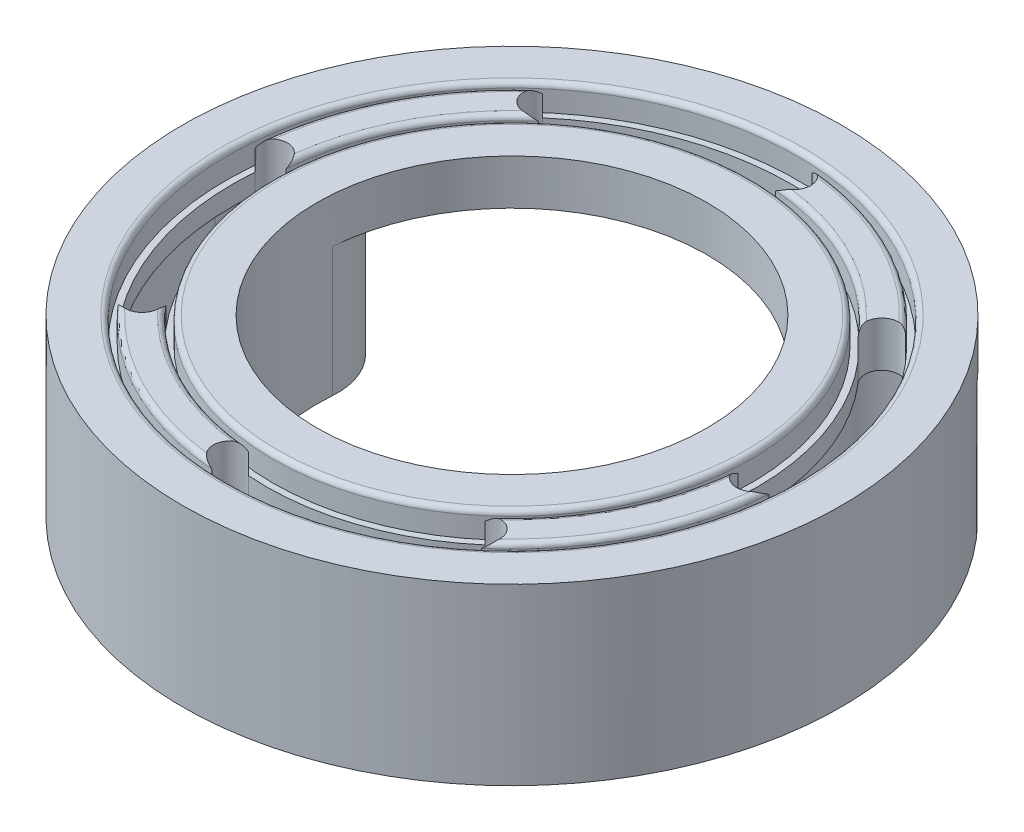
SolidWorks part; units mm, degrees
ref_plane "前视基准面" through (0, 0, 0) normal (0, 0, 1) x (1, 0, 0)
ref_plane "上视基准面" through (0, 0, 0) normal (0, 1, 0) x (1, 0, 0)
ref_plane "右视基准面" through (0, 0, 0) normal (1, 0, 0) x (0, 0, -1)
other "Configuration Table"
sketch "草图1" plane through (0, 0, 0) normal (0, 1, 0) x (1, 0, 0)
  circle A0 centre (0, 0) radius 25.5
extrude "凸台-拉伸1" add sketch "草图1" along normal blind 3.5
sketch "草图2" plane through (0, 3.5, 0) normal (0, 1, 0) x (1, 0, 0)
  circle A0 centre (0, 0) radius 19
  circle A1 centre (0, 0) radius 18.5
  dimension "D1" = 0.5
  dimension "D2" = 37
extrude "切除-拉伸1" cut sketch "草图2" against normal blind 2
sketch "草图3" plane through (0, 3.5, 0) normal (0, 1, 0) x (1, 0, 0)
  circle A0 centre (0, 0) radius 22.1
  circle A1 centre (0, 0) radius 21.6
  dimension "D1" = 0.5
  dimension "D2" = 43.2
extrude "切除-拉伸2" cut sketch "草图3" against normal blind 2
fillet "圆角1" radius 0.4 4 edges at (0, 3.5, 18.5) (0, 3.5, 19) (0, 3.5, 21.6) (0, 3.5, 22.1)
sketch "草图4" plane through (0, 0, 0) normal (0, -1, 0) x (1, 0, 0)
  circle A0 centre (0, 0) radius 19 construction
  circle A1 centre (0, 0) radius 21.6 construction
  arc A2 (-18.0617, 5.8972) -> (-18.9435, -1.4636) centre (0, 0) ccw
  arc A3 (-20.5333, 6.7041) -> (-21.5358, -1.6639) centre (0, 0) ccw
  arc A4 (-21.5358, -1.6639) -> (-18.9435, -1.4636) centre (-20.2397, -1.5638) ccw
  arc A8 (-1.6639, 21.5358) -> (-1.4636, 18.9435) centre (-1.5638, 20.2397) ccw
  arc A12 (21.5358, 1.6639) -> (18.9435, 1.4636) centre (20.2397, 1.5638) ccw
  arc A16 (1.6639, -21.5358) -> (1.4636, -18.9435) centre (1.5638, -20.2397) ccw
  arc A20 (-20.5333, 6.7041) -> (-16.4047, 14.0516) centre (0, 0) cw
  arc A21 (-18.0617, 5.8972) -> (-14.43, 12.3602) centre (0, 0) cw
  arc A22 (-12.3602, -14.43) -> (1.4636, -18.9435) centre (0, 0) ccw
  arc A23 (-14.0516, -16.4047) -> (1.6639, -21.5358) centre (0, 0) ccw
  arc A24 (-14.0516, -16.4047) -> (-12.3602, -14.43) centre (-13.2059, -15.4174) cw
  arc A26 (18.0617, -5.8972) -> (18.9435, 1.4636) centre (0, 0) ccw
  arc A27 (20.5333, -6.7041) -> (21.5358, 1.6639) centre (0, 0) ccw
  arc A28 (-16.4047, 14.0516) -> (-14.43, 12.3602) centre (-15.4174, 13.2059) cw
  arc A29 (14.0516, 16.4047) -> (12.3602, 14.43) centre (13.2059, 15.4174) cw
  arc A30 (12.3602, 14.43) -> (-1.4636, 18.9435) centre (0, 0) ccw
  arc A31 (14.0516, 16.4047) -> (-1.6639, 21.5358) centre (0, 0) ccw
  arc A33 (16.4047, -14.0516) -> (14.43, -12.3602) centre (15.4174, -13.2059) cw
  circle A34 centre (-13.2059, -15.4174) radius 1.3 [skipped]
  circle A35 centre (-18.1006, -9.1901) radius 1.3 [skipped]
  circle A36 centre (15.4174, -13.2059) radius 1.3 [skipped]
  circle A37 centre (9.1901, -18.1006) radius 1.3 [skipped]
  circle A38 centre (13.2059, 15.4174) radius 1.3 [skipped]
  circle A39 centre (18.1006, 9.1901) radius 1.3 [skipped]
  circle A40 centre (-15.4174, 13.2059) radius 1.3 [skipped]
  circle A41 centre (-9.1901, 18.1006) radius 1.3 [skipped]
  arc A42 (20.5333, -6.7041) -> (16.4047, -14.0516) centre (0, 0) cw
  arc A43 (18.0617, -5.8972) -> (14.43, -12.3602) centre (0, 0) cw
  arc A44 (-18.0617, 5.8972) -> (-20.5333, 6.7041) centre (-19.2975, 6.3007) ccw [skipped]
  arc A45 (6.7041, 20.5333) -> (5.8972, 18.0617) centre (6.3007, 19.2975) ccw [skipped]
  arc A46 (18.0617, -5.8972) -> (20.5333, -6.7041) centre (19.2975, -6.3007) ccw [skipped]
  arc A47 (-5.8972, -18.0617) -> (-6.7041, -20.5333) centre (-6.3007, -19.2975) ccw [skipped]
  point P40 (0, 0)
  dimension "D1" = 16
extrude "切除-拉伸5" cut sketch "草图4" against normal through all
sketch "草图5" plane through (0, 0, 0) normal (0, -1, 0) x (1, 0, 0)
  arc A0 (19.3666, -16.5886) -> (-25.4242, -1.9643) centre (0, 0) ccw
  arc A1 (-25.4242, -1.9643) -> (-15.0551, -1.1632) centre (-20.2397, -1.5638) ccw
  arc A2 (11.4681, -9.8231) -> (-15.0551, -1.1632) centre (0, 0) ccw
  arc A3 (11.4681, -9.8231) -> (19.3666, -16.5886) centre (15.4174, -13.2059) ccw
  arc A4 (18.9869, -16.2634) -> (-24.9257, -1.9258) centre (0, 0) ccw
  arc A5 (-24.9257, -1.9258) -> (-15.5536, -1.2017) centre (-20.2397, -1.5638) ccw
  arc A6 (11.8478, -10.1483) -> (-15.5536, -1.2017) centre (0, 0) ccw
  arc A7 (11.8478, -10.1483) -> (18.9869, -16.2634) centre (15.4174, -13.2059) ccw
  dimension "D1" = 0.5
extrude "凸台-拉伸2" add sketch "草图5" along normal blind 10
sketch "草图6" plane through (0, 0, 0) normal (0, -1, 0) x (1, 0, 0)
  arc A0 (11.4681, -9.8231) -> (-15.0551, -1.1632) centre (0, 0) ccw construction
  circle A2 centre (0, 0) radius 15.1
extrude "切除-拉伸6" cut sketch "草图6" against normal blind 10
